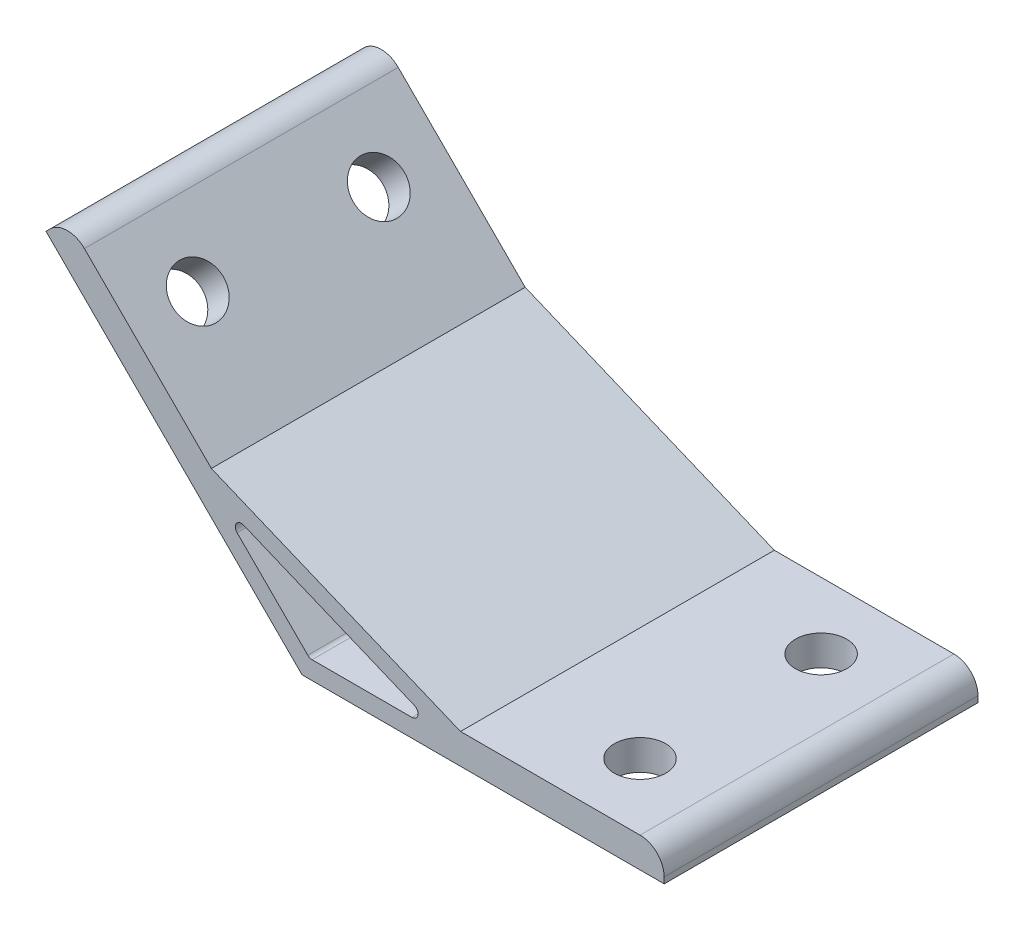
SolidWorks part; units mm, degrees
material "6063 T5"
ref_plane "Спереди" through (0, 0, 0) normal (0, 0, 1) x (1, 0, 0)
ref_plane "Сверху" through (0, 0, 0) normal (0, 1, 0) x (1, 0, 0)
ref_plane "Справа" through (0, 0, 0) normal (1, 0, 0) x (0, 0, -1)
sketch "Эскиз1" plane through (0, 0, 0) normal (0, 0, 1) x (1, 0, 0)
  line L0 (0, 0) -> (-42.4264, 42.4264)
  line L1 (-42.4264, 42.4264) -> (-38.8909, 45.9619)
  line L2 (-38.8909, 45.9619) -> (-15.0286, 22.0996)
  line L3 (-15.0286, 22.0996) -> (26.2536, 5)
  line L4 (26.2536, 5) -> (60, 5)
  line L5 (60, 5) -> (60, 0)
  line L6 (60, 0) -> (0, 0)
  line L7 (-14.3137, 18.5563) -> (23.2426, 3)
  line L8 (23.2426, 3) -> (1.2426, 3)
  line L9 (1.2426, 3) -> (-14.3137, 18.5563)
  line L10 (12.2426, 3) -> (12.2426, 0) construction
  line L11 (-6.5355, 10.7782) -> (-8.6569, 8.6569) construction
  line L12 (0, 0) -> (4.4645, 10.7782) construction
  dimension "D1" = 60
  dimension "D2" = 135
  dimension "D3" = 3
  dimension "D4" = 5
  dimension "D5" = 3
  dimension "D6" = 22
extrude "Бобышка-Вытянуть1" add sketch "Эскиз1" along normal mid plane 52
sketch "Эскиз2" plane through (0, 0, 0) normal (-0.7071, -0.7071, 0) x (0, 0, 1)
  line L0 (26, 60) -> (-26, 60) construction
  line L1 (-15, 45) -> (15, 45) construction
  line L2 (-26, 60) -> (-26, 0) construction
  circle A0 centre (-15, 45) radius 4.25
  circle A1 centre (15, 45) radius 4.25
  point P2 (0, 45)
  dimension "D1" = 8.5
  dimension "D2" = 15
  dimension "D4" = 11
  dimension "D3" = 30
extrude "Вырез-Вытянуть1" cut sketch "Эскиз2" against normal up to surface (5 mm away) up to face at (-26.9597, 34.0308, 0)
sketch "Эскиз3" plane through (0, 0, 0) normal (0, -1, 0) x (1, 0, 0)
  line L0 (60, 26) -> (60, -26) construction
  line L1 (45, 15) -> (45, -15) construction
  circle A0 centre (45, 15) radius 4.25
  circle A1 centre (45, -15) radius 4.25
  point P2 (45, 0)
  dimension "D1" = 8.5
  dimension "D2" = 15
  dimension "D3" = 30
extrude "Вырез-Вытянуть2" cut sketch "Эскиз3" against normal up to surface (5 mm away) up to face at (43.1268, 5, 0)
fillet "Скругление1" radius 4 2 edges at (60, 5, 0) (-38.8909, 45.9619, 0)
fillet "Скругление2" radius 1 3 edges at (-14.3137, 18.5563, 0) (1.2426, 3, 0) (23.2426, 3, 0)
